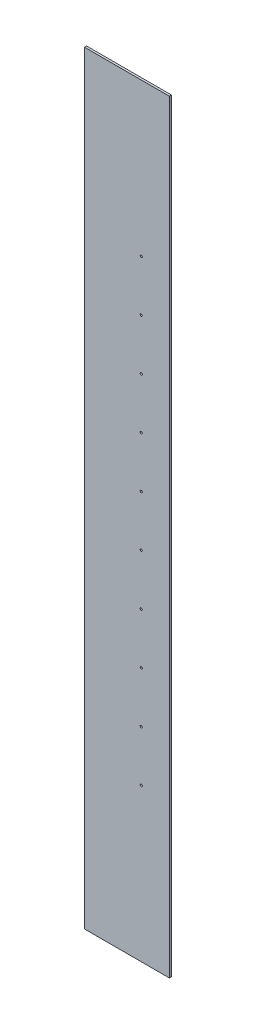
SolidWorks part; units mm, degrees
ref_plane "Front Plane" through (0, 0, 0) normal (0, 0, 1) x (1, 0, 0)
ref_plane "Top Plane" through (0, 0, 0) normal (0, 1, 0) x (1, 0, 0)
ref_plane "Right Plane" through (0, 0, 0) normal (1, 0, 0) x (0, 0, -1)
sketch "Sketch1" plane through (0, 0, 0) normal (0, 0, 1) x (1, 0, 0)
  line L1 (100, -900) -> (-100, -900)
  line L2 (100, -900) -> (100, 900)
  line L3 (100, 900) -> (-100, 900)
  line L4 (-100, -900) -> (-100, 900)
  circle A0 centre (33.7, -540) radius 2.5
  circle A1 centre (33.7, -420) radius 2.5
  circle A2 centre (33.7, -300) radius 2.5
  circle A3 centre (33.7, -180) radius 2.5
  circle A4 centre (33.7, -60) radius 2.5
  circle A5 centre (33.7, 60) radius 2.5
  circle A6 centre (33.7, 180) radius 2.5
  circle A7 centre (33.7, 300) radius 2.5
  circle A8 centre (33.7, 420) radius 2.5
  circle A9 centre (33.7, 540) radius 2.5
  point P0 (0, 0)
  dimension "D1" = 66.3
  dimension "D3" = 5
  dimension "D2" = 10
  dimension "D4" = 360
  dimension "D5" = 200
extrude "Boss-Extrude1" add sketch "Sketch1" along normal blind 5
